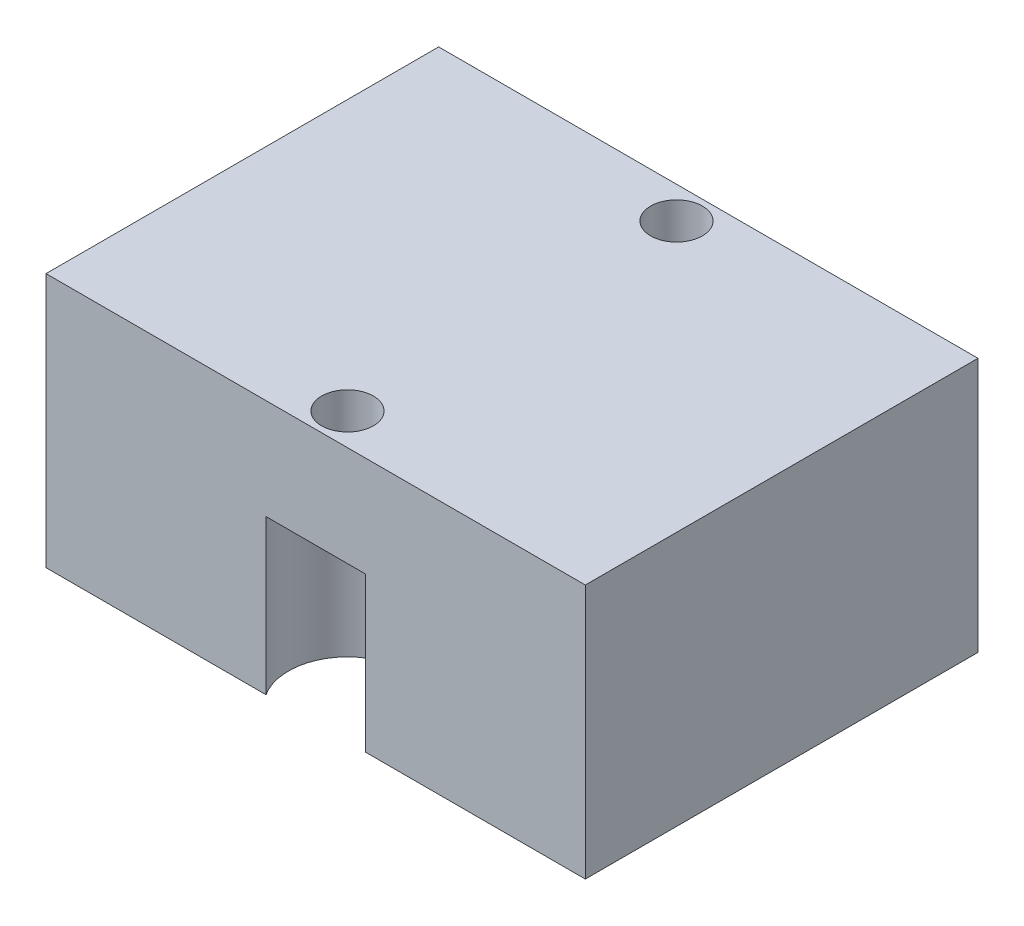
SolidWorks part; units mm, degrees
ref_plane "Front Plane" through (0, 0, 0) normal (0, 0, 1) x (1, 0, 0)
ref_plane "Top Plane" through (0, 0, 0) normal (0, 1, 0) x (1, 0, 0)
ref_plane "Right Plane" through (0, 0, 0) normal (1, 0, 0) x (0, 0, -1)
sketch "Sketch1" plane through (0, 0, 0) normal (0, 1, 0) x (1, 0, 0)
  line L1 (0, 0) -> (25.41, 0)
  line L2 (0, 0) -> (0, 18.5)
  line L3 (0, 18.5) -> (25.41, 18.5)
  line L4 (25.41, 0) -> (25.41, 18.5)
extrude "Boss-Extrude1" add sketch "Sketch1" along normal blind 12
sketch "Sketch2" plane through (0, 0, 0) normal (0, -1, 0) x (1, 0, 0)
  line L0 (0, 0) -> (1.5, 0)
  line L1 (0, 0) -> (25.41, 0) construction
  line L2 (1.5, 0) -> (1.5, -18.5)
  line L3 (25.41, -18.5) -> (0, -18.5) construction
  line L4 (25.41, 0) -> (23.91, 0)
  line L5 (23.91, 0) -> (23.91, -18.5)
  line L6 (0, 0) -> (0, -1.5)
  line L7 (0, -18.5) -> (0, 0) construction
  line L8 (0, -1.5) -> (25.41, -1.5)
  line L9 (25.41, 0) -> (25.41, -18.5) construction
  line L10 (0, -18.5) -> (0, -17)
  line L11 (0, -17) -> (25.41, -17)
hole_wizard "#2-56 Tapped Hole1" positions "Sketch3" profile "Sketch4" tap size "#2-56" standard "ANSI Inch"
sketch "Sketch3" plane through (0, 0, 0) normal (0, -1, 0) x (-1, 0, 0)
  line L0 (-23.91, 0) -> (-23.91, 18.5) construction
  line L1 (0, 17) -> (-25.41, 17) construction
  line L2 (0, 1.5) -> (-25.41, 1.5) construction
  line L3 (-1.5, 0) -> (-1.5, 18.5) construction
  point P0 (-23.91, 17)
  point P6 (-23.91, 1.5)
  point P10 (-1.5, 1.5)
  point P14 (-1.5, 17)
sketch "Sketch4" plane through (23.91, 0, -17) normal (1, 0, 0) x (0, 0, -1)
  line L0 (0, 0) -> (0, 8)
  line L1 (0, 8) -> (0.889, 7.4658)
  line L2 (0.889, 7.4658) -> (0.889, 0)
  line L5 (0.889, 0) -> (0, 0)
  line L10 (0, 8) -> (-0.889, 7.4658) construction
  line L11 (0, -6.35) -> (0, 107.95) construction
  dimension "Tap Drill Dia." = 1.778
  dimension "Tap Drill Depth" = 8
  dimension "Drill Angle" = 118
cosmetic thread "Hole Thread1" parameters "D1"=4.37, "D2"=2.1844
cosmetic thread "Hole Thread2" parameters "D1"=4.37, "D2"=2.1844
cosmetic thread "Hole Thread3" parameters "D1"=4.37, "D2"=2.1844
cosmetic thread "Hole Thread4" parameters "D1"=4.37, "D2"=2.1844
sketch "Sketch5" plane through (0, 0, 0) normal (0, -1, 0) x (1, 0, 0)
  circle A0 centre (12.705, -9.25) radius 3
extrude "Cut-Extrude1" cut sketch "Sketch5" against normal blind 3
sketch "Sketch6" plane through (0, 0, 0) normal (0, -1, 0) x (1, 0, 0)
  line L0 (0, -9.25) -> (25.41, -9.25)
  line L1 (0, -18.5) -> (0, 0) construction
  line L2 (25.41, 0) -> (25.41, -18.5) construction
  line L3 (0, -9.25) -> (5, -9.25)
  line L4 (25.41, -9.25) -> (20.41, -9.25)
sketch "Sketch11" plane through (0, 0, 0) normal (0, -1, 0) x (1, 0, 0)
  line L0 (12.705, 0) -> (12.705, -18.5)
  line L1 (0, 0) -> (25.41, 0) construction
  line L2 (25.41, -18.5) -> (0, -18.5) construction
  line L3 (12.705, -18.5) -> (12.705, -17)
  line L4 (12.705, 0) -> (12.705, -1.5)
  point P6 (0, 0)
  point P9 (0, 0)
  point P10 (12.705, -17.1716)
  point P11 (12.705, -1.7075)
hole_wizard "CBORE for #2 Binding Head Machine Screw3" positions "Sketch12" profile "Sketch13" counterbore size "#2" standard "ANSI Inch" end condition through all
sketch "Sketch12" plane through (0, 0, 0) normal (0, -1, 0) x (-1, 0, 0)
  point P0 (-12.705, 17)
  point P3 (-12.705, 1.5)
sketch "Sketch13" plane through (12.705, 0, -17) normal (1, 0, 0) x (0, 0, -1)
  line L0 (0, 0) -> (0, 12)
  line L1 (0, 12) -> (1.2192, 12)
  line L3 (1.2192, 12) -> (1.2192, 7.27)
  line L4 (1.2192, 7.27) -> (2.7788, 7.27)
  line L5 (2.7788, 7.27) -> (2.7788, 0)
  line L7 (2.7788, 0) -> (0, 0)
  line L11 (0, -6.35) -> (0, 107.95) construction
  dimension "Thru Hole Dia." = 2.4384
  dimension "Thru Hole Depth" = 12
  dimension "C'Bore Dia." = 5.5575
  dimension "C'Bore Depth" = 7.27
